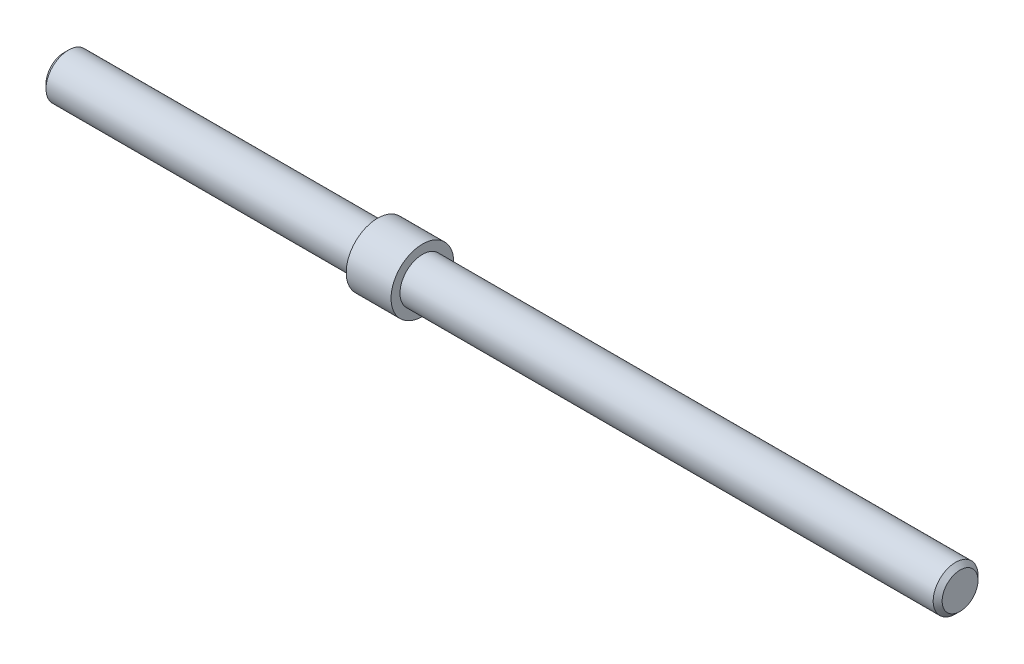
SolidWorks part; units mm, degrees
ref_plane "Front Plane" through (0, 0, 0) normal (0, 0, 1) x (1, 0, 0)
ref_plane "Top Plane" through (0, 0, 0) normal (0, 1, 0) x (1, 0, 0)
ref_plane "Right Plane" through (0, 0, 0) normal (1, 0, 0) x (0, 0, -1)
sketch "Sketch1" plane through (0, 0, 0) normal (1, 0, 0) x (0, 0, -1)
  circle A0 centre (0, 0) radius 5
  dimension "D1" = 10
extrude "Boss-Extrude1" add sketch "Sketch1" along normal blind 200
chamfer "Chamfer1" distance 1 angle 45 2 edges at (0, 0, -5) (200, 0, -5)
sketch "Sketch2" plane through (0, 0, 0) normal (1, 0, 0) x (0, 0, -1)
  circle A0 centre (0, 0) radius 7
  dimension "D1" = 14
extrude "Boss-Extrude2" add sketch "Sketch2" along normal blind 10 from offset 70
